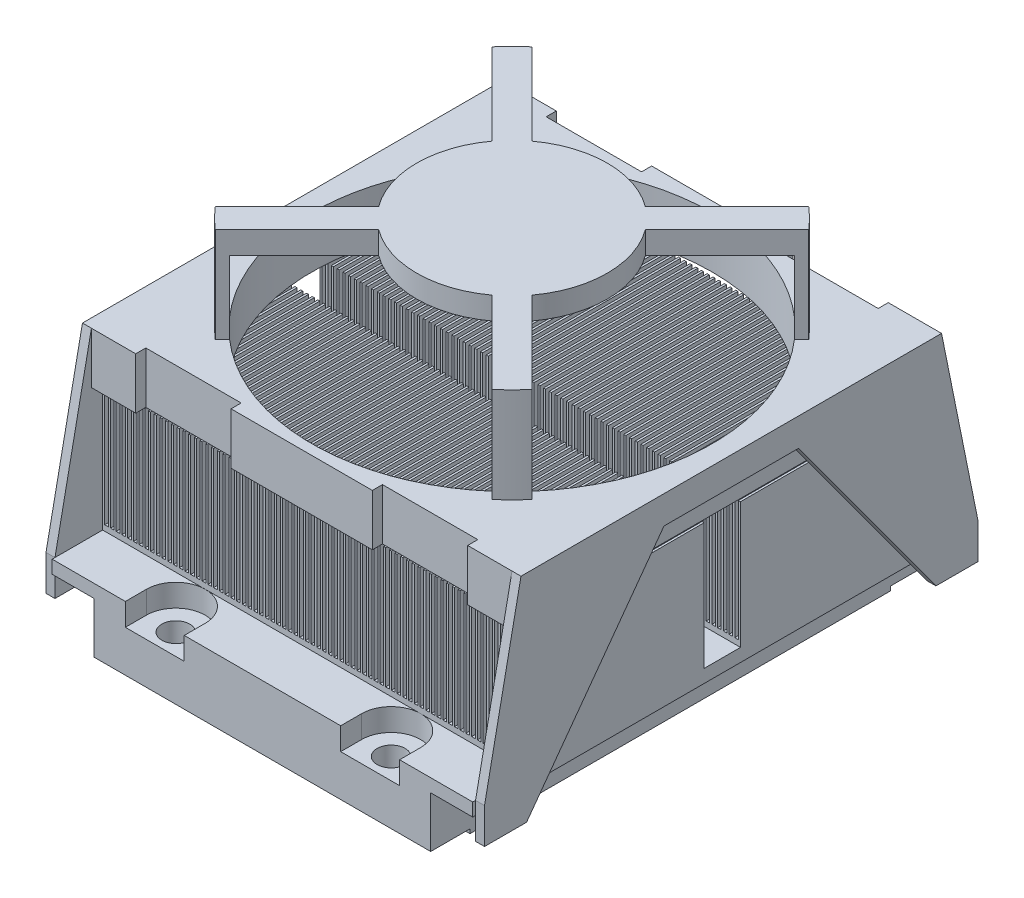
SolidWorks part; units mm, degrees
material "Copper"
ref_plane "Front Plane" through (0, 0, 0) normal (0, 0, 1) x (1, 0, 0)
ref_plane "Top Plane" through (0, 0, 0) normal (0, 1, 0) x (1, 0, 0)
ref_plane "Right Plane" through (0, 0, 0) normal (1, 0, 0) x (0, 0, -1)
sketch "Sketch1" plane through (0, 0, 0) normal (0, 1, 0) x (1, 0, 0)
  line L1 (-37.5, -44.5) -> (37.5, -44.5)
  line L2 (-37.5, -44.5) -> (-37.5, 44.5)
  line L3 (-37.5, 44.5) -> (37.5, 44.5)
  line L4 (37.5, -44.5) -> (37.5, 44.5)
  line L5 (-37.5, -44.5) -> (37.5, 44.5) construction
  line L6 (-37.5, 44.5) -> (37.5, -44.5) construction
  point P0 (0, 0)
  dimension "D1" = 89
  dimension "D2" = 75
extrude "Boss-Extrude1" add sketch "Sketch1" along normal blind 12.15
sketch "Sketch2" plane through (0, 0, 0) normal (0, -1, 0) x (1, 0, 0)
  line L0 (37.5, -44.5) -> (-37.5, -44.5) construction
  line L1 (-37.5, 44.5) -> (-30, 44.5)
  line L2 (-37.5, 44.5) -> (-37.5, -44.5)
  line L3 (-37.5, -44.5) -> (-30, -44.5)
  line L4 (-30, 44.5) -> (-30, -44.5)
  line L5 (0, 44.5) -> (0, -44.5) construction
  line L6 (-37.5, 44.5) -> (37.5, 44.5) construction
  line L7 (37.5, -44.5) -> (30, -44.5)
  line L8 (30, 44.5) -> (30, -44.5)
  line L9 (37.5, 44.5) -> (30, 44.5)
  line L10 (37.5, 44.5) -> (37.5, -44.5)
  dimension "D1" = 7.5
extrude "Cut-Extrude1" cut sketch "Sketch2" against normal offset from surface (9.82 mm away) 2.33 up to face at (0, 12.15, 0)
sketch "Sketch3" plane through (0, 0, 0) normal (0, -1, 0) x (1, 0, 0)
  line L0 (30, -44.5) -> (30, 44.5) construction
  line L1 (-30, 44.5) -> (30, 44.5)
  line L2 (-30, 44.5) -> (-30, 37.5)
  line L3 (-30, 37.5) -> (30, 37.5)
  line L4 (30, 44.5) -> (30, 37.5)
  line L5 (-30, 0) -> (30, 0) construction
  line L6 (-30, -44.5) -> (-30, 44.5) construction
  line L7 (-30, -37.5) -> (30, -37.5)
  line L8 (30, -44.5) -> (30, -37.5)
  line L9 (-30, -44.5) -> (30, -44.5)
  line L10 (-30, -44.5) -> (-30, -37.5)
  dimension "D1" = 7
extrude "Cut-Extrude2" cut sketch "Sketch3" against normal blind 0.75
sketch "Sketch4" plane through (0, 0.75, 0) normal (0, -1, 0) x (1, 0, 0)
  line L0 (-19.2, 40.75) -> (19.2, 40.75) construction
  line L1 (0, 44.5) -> (0, -44.5) construction
  line L4 (-30, 0) -> (30, 0) construction
  line L5 (-30, 44.5) -> (-30, -44.5) construction
  line L6 (30, -44.5) -> (30, 44.5) construction
  line L7 (30, 44.5) -> (-30, 44.5) construction
  line L8 (-30, -44.5) -> (30, -44.5) construction
  circle A0 centre (-19.2, 40.75) radius 2.5
  circle A1 centre (19.2, 40.75) radius 2.5
  circle A2 centre (19.2, -40.75) radius 2.5
  circle A3 centre (-19.2, -40.75) radius 2.5
  point P10 (0, 40.75)
  point P21 (0, 0)
  dimension "D2" = 5
  dimension "D3" = 81.5
  dimension "D1" = 38.4
extrude "Cut-Extrude3" cut sketch "Sketch4" against normal through all
sketch "Sketch5" plane through (0, 12.15, 0) normal (0, 1, 0) x (1, 0, 0)
  line L0 (-24.45, 40.75) -> (-24.45, 44.5)
  line L1 (37.5, 44.5) -> (-37.5, 44.5) construction
  line L2 (-13.95, 40.75) -> (-13.95, 44.5)
  line L3 (-24.45, 44.5) -> (-13.95, 44.5)
  line L4 (0, 44.5) -> (0, -44.5) construction
  line L5 (-37.5, -44.5) -> (37.5, -44.5) construction
  line L6 (-37.5, 0) -> (37.5, 0) construction
  line L7 (-37.5, 44.5) -> (-37.5, -44.5) construction
  line L8 (37.5, -44.5) -> (37.5, 44.5) construction
  line L9 (24.45, 40.75) -> (24.45, 44.5)
  line L10 (13.95, 40.75) -> (13.95, 44.5)
  line L11 (24.45, 44.5) -> (13.95, 44.5)
  line L12 (13.95, -40.75) -> (13.95, -44.5)
  line L13 (24.45, -44.5) -> (13.95, -44.5)
  line L14 (24.45, -40.75) -> (24.45, -44.5)
  line L15 (-24.45, -40.75) -> (-24.45, -44.5)
  line L16 (-13.95, -40.75) -> (-13.95, -44.5)
  line L17 (-24.45, -44.5) -> (-13.95, -44.5)
  arc A0 (-24.45, 40.75) -> (-13.95, 40.75) centre (-19.2, 40.75) ccw
  arc A1 (24.45, 40.75) -> (13.95, 40.75) centre (19.2, 40.75) cw
  arc A2 (24.45, -40.75) -> (13.95, -40.75) centre (19.2, -40.75) ccw
  arc A3 (-24.45, -40.75) -> (-13.95, -40.75) centre (-19.2, -40.75) cw
  dimension "D1" = 10.5
extrude "Cut-Extrude4" cut sketch "Sketch5" against normal blind 4
sketch "Sketch6" plane through (0, 12.15, 0) normal (0, 1, 0) x (1, 0, 0)
  line L0 (-37.5, 44.5) -> (-37.5, -44.5) construction
  line L1 (-37.5, 35.5) -> (37.5, 35.5)
  line L2 (-37.5, 35.5) -> (-37.5, 3.25)
  line L3 (-37.5, 3.25) -> (37.5, 3.25)
  line L4 (37.5, 35.5) -> (37.5, 3.25)
  line L5 (37.5, -44.5) -> (37.5, 44.5) construction
  line L6 (-24.45, 44.5) -> (-37.5, 44.5) construction
  dimension "D1" = 9
  dimension "D2" = 32.25
extrude "Boss-Extrude2" add sketch "Sketch6" along normal blind 1
sketch "Sketch7" plane through (0, 13.15, 0) normal (0, 1, 0) x (1, 0, 0)
  line L5 (-37.5, 3.25) -> (37.5, 3.25) construction
  line L6 (-37.5, 35.5) -> (-37.125, 35.5)
  line L7 (-37.5, 35.5) -> (-37.5, 3.25)
  line L8 (-37.5, 3.25) -> (-37.125, 3.25)
  line L9 (-37.125, 35.5) -> (-37.125, 3.25)
  dimension "D1" = 0.375
extrude "Boss-Extrude3" add sketch "Sketch7" along normal blind 21.5
pattern_linear "LPattern2" count 74 spacing 1.0223 along (1, 0, 0) of "Boss-Extrude3"
ref_plane "Plane1" through (0, 0, 0) normal (0, 0, -1) x (-1, 0, 0)
mirror "Mirror1" about plane through (0, 0, 0) normal (0, 0, -1) of "Boss-Extrude2", "LPattern2", "Boss-Extrude3"
sketch "Sketch8" plane through (-37.5, 0, 0) normal (-1, 0, 0) x (0, 0, 1)
  line L0 (-44.5, 9.82) -> (-44.5, 0.75) construction
  line L1 (-44.5, 5.82) -> (44.5, 5.82) construction
  line L2 (-44.5, 5.82) -> (-44.5, 44.32) construction
  line L3 (-44.5, 44.32) -> (44.5, 44.32) construction
  line L4 (44.5, 5.82) -> (44.5, 44.32) construction
  line L5 (-44.5, 9.82) -> (44.5, 9.82) construction
  line L7 (-44, 12.15) -> (-37.5, 44.32)
  line L8 (-37.5, 44.32) -> (37.5, 44.32)
  line L9 (0, 44.32) -> (0, 5.82) construction
  line L11 (-36.5, 5.82) -> (-12, 39.32)
  line L12 (-12, 39.32) -> (12, 39.32)
  line L13 (36.5, 5.82) -> (12, 39.32)
  line L16 (44, 12.15) -> (37.5, 44.32)
  line L17 (-44.5, 12.15) -> (-35.5, 12.15) construction
  line L18 (-44, 12.15) -> (-44, 5.82)
  line L19 (-44, 5.82) -> (-36.5, 5.82)
  line L20 (44, 5.82) -> (36.5, 5.82)
  line L21 (44, 12.15) -> (44, 5.82)
  point P7 (0, 0)
  point P21 (0, 39.32)
  dimension "D1" = 4
  dimension "D2" = 38.5
  dimension "D3" = 37.5
  dimension "D4" = 5
  dimension "D5" = 8
  dimension "D6" = 12
  dimension "D7" = 0.5
extrude "Boss-Extrude4" add sketch "Sketch8" along normal blind 1.6
ref_plane "Plane2" through (0, 0, 0) normal (1, 0, 0) x (0, 0, -1)
mirror "Mirror2" about plane through (0, 0, 0) normal (1, 0, 0) of "Boss-Extrude4"
sketch "Sketch9" plane through (0, 44.32, 0) normal (0, 1, 0) x (1, 0, 0)
  line L0 (-39.1, -37.5) -> (-39.1, 37.5) construction
  line L1 (-37.5, 37.5) -> (-29.6, 37.5)
  line L2 (-37.5, 37.5) -> (-37.5, -37.5)
  line L3 (-37.5, -37.5) -> (-29.6, -37.5)
  line L4 (37.5, 37.5) -> (37.5, -37.5)
  line L6 (-29.6, 37.5) -> (-29.6, 35.7)
  line L8 (29.6, 37.5) -> (29.6, 35.7)
  line L9 (0, 37.5) -> (0, -35.7709) construction
  line L10 (29.6, 37.5) -> (37.5, 37.5)
  line L11 (-37.5, 0) -> (37.5, 0) construction
  line L15 (29.6, -37.5) -> (37.5, -37.5)
  line L16 (-29.6, 35.7) -> (-12.6, 35.7)
  line L17 (-12.6, 35.7) -> (-12.6, 37.5)
  line L18 (-12.6, 37.5) -> (12.6, 37.5)
  line L19 (12.6, 37.5) -> (12.6, 35.7)
  line L20 (12.6, 35.7) -> (29.6, 35.7)
  line L21 (29.6, -37.5) -> (29.6, -35.7)
  line L22 (12.6, -35.7) -> (29.6, -35.7)
  line L23 (-12.6, -37.5) -> (12.6, -37.5)
  line L24 (12.6, -37.5) -> (12.6, -35.7)
  line L25 (-12.6, -35.7) -> (-12.6, -37.5)
  line L26 (-29.6, -35.7) -> (-12.6, -35.7)
  line L27 (-29.6, -37.5) -> (-29.6, -35.7)
  point P12 (0, 35.7)
  dimension "D1" = 9.5
  dimension "D2" = 17
  dimension "D3" = 1.8
extrude "Boss-Extrude5" add sketch "Sketch9" against normal offset from surface (9.17 mm away) 0.5 up to face at (-20.9563, 34.65, 19.375)
sketch "Sketch10" plane through (0, 44.32, 0) normal (0, 1, 0) x (1, 0, 0)
  circle A0 centre (0, 0) radius 37.5
  dimension "D1" = 75
extrude "Boss-Extrude6" add sketch "Sketch10" along normal blind 17
sketch "Sketch11" plane through (0, 35.15, 0) normal (0, -1, 0) x (1, 0, 0)
  circle A2 centre (0, 0) radius 35.7
  circle A3 centre (0, 0) radius 35.7
  dimension "D1" = 1.8
extrude "Cut-Extrude5" cut sketch "Sketch11" against normal offset from surface (22.17 mm away) 4 up to face at (0, 61.32, 37.5)
sketch "Sketch12" plane through (0, 61.32, 0) normal (0, 1, 0) x (1, 0, 0)
  line L0 (26.5165, 26.5165) -> (0, 0) construction
  line L1 (-48.0121, 0) -> (57.2648, 0) construction
  line L2 (13.6579, 10.1224) -> (28.2253, 24.6897)
  line L3 (10.1224, 13.6579) -> (24.6897, 28.2253)
  line L4 (10.1224, -13.6579) -> (24.6897, -28.2253)
  line L5 (13.6579, -10.1224) -> (28.2253, -24.6897)
  line L6 (-13.6579, -10.1224) -> (-28.2253, -24.6897)
  line L7 (-10.1224, -13.6579) -> (-24.6897, -28.2253)
  line L8 (-10.1224, 13.6579) -> (-24.6897, 28.2253)
  line L9 (-13.6579, 10.1224) -> (-28.2253, 24.6897)
  line L10 (-39.4649, 39.4649) -> (39.8173, -39.8173) construction
  circle A0 centre (0, 0) radius 37.5 construction
  arc A1 (-10.1224, -13.6579) -> (10.1224, -13.6579) centre (0, 0) ccw
  arc A4 (28.2253, -24.6897) -> (28.2253, 24.6897) centre (0, 0) ccw
  arc A6 (24.6897, 28.2253) -> (-24.6897, 28.2253) centre (0, 0) ccw
  arc A7 (-28.2253, 24.6897) -> (-28.2253, -24.6897) centre (0, 0) ccw
  arc A8 (-24.6897, -28.2253) -> (24.6897, -28.2253) centre (0, 0) ccw
  arc A9 (-13.6579, 10.1224) -> (-13.6579, -10.1224) centre (0, 0) ccw
  arc A10 (10.1224, 13.6579) -> (-10.1224, 13.6579) centre (0, 0) ccw
  arc A11 (13.6579, -10.1224) -> (13.6579, 10.1224) centre (0, 0) ccw
  point P5 (44.3733, -34.735)
  point P6 (0, 0)
  dimension "D1" = 34
  dimension "D2" = 45
  dimension "D3" = 5
  dimension "D4" = 4
extrude "Cut-Extrude6" cut sketch "Sketch12" against normal up to surface (17 mm away)
